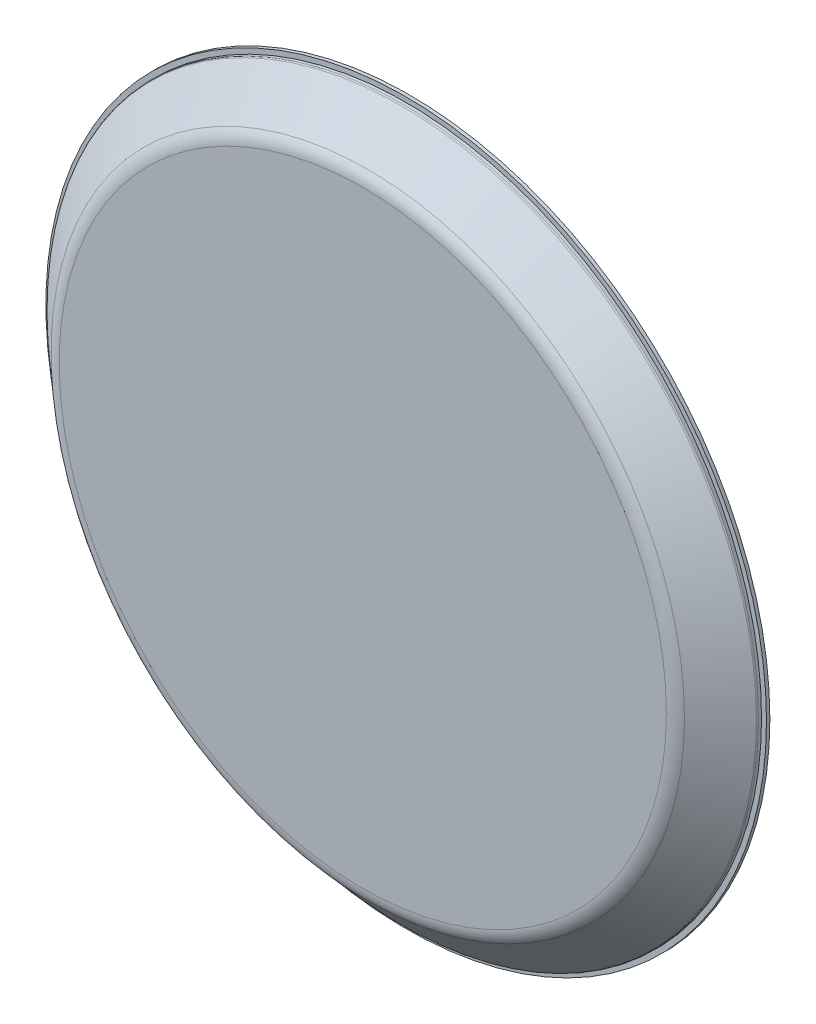
SolidWorks part; units mm, degrees
ref_plane "Front Plane" through (0, 0, 0) normal (0, 0, 1) x (1, 0, 0)
ref_plane "Top Plane" through (0, 0, 0) normal (0, 1, 0) x (1, 0, 0)
ref_plane "Right Plane" through (0, 0, 0) normal (1, 0, 0) x (0, 0, -1)
sketch "Sketch1" plane through (0, 0, 0) normal (1, 0, 0) x (0, 0, -1)
  line L0 (0, 70.8819) -> (0, -77.1698) construction
  line L1 (0.2, 18.2509) -> (0.3685, 18.2536)
  line L2 (0.3685, 18.2536) -> (0.3685, 17.5642)
  line L3 (-1.2984, 15.6582) -> (0.3431, 17.4976)
  line L4 (-1.4, 15.3919) -> (-1.4, 0)
  line L5 (-1.4, 0) -> (-2, 0)
  line L6 (-2, 0) -> (-2, 15.3776)
  line L7 (-1.7461, 16.0434) -> (-0.0297, 17.9668)
  line L8 (-10.6441, 0) -> (9.8244, 0) construction
  line L10 (0.0445, 18.0002) -> (0.2, 18.0009)
  line L11 (0.2, 18.0009) -> (0.2, 18.2509)
  line L20 (-2, 20.3) -> (-2, -6.7828) construction
  arc A0 (-2, 15.3776) -> (-1.7461, 16.0434) centre (-1, 15.3776) cw
  arc A1 (-1.2984, 15.6582) -> (-1.4, 15.3919) centre (-1, 15.3919) ccw
  arc A2 (-0.0297, 17.9668) -> (0.0445, 18.0002) centre (0.045, 17.9002) cw
  arc A3 (0.3685, 17.5642) -> (0.3431, 17.4976) centre (0.2685, 17.5642) cw
  point P16 (0, 0)
  point P19 (0, 18)
  dimension "D3" = 1
  dimension "D4" = 0.4
  dimension "D7" = 0.1
  dimension "D8" = 0.1
  dimension "D1" = 0.2
  dimension "D2" = 0.6
  dimension "D5" = 0.25
  dimension "D6" = 2
revolve "Revolve1" add sketch "Sketch1" angle 360 about L8
